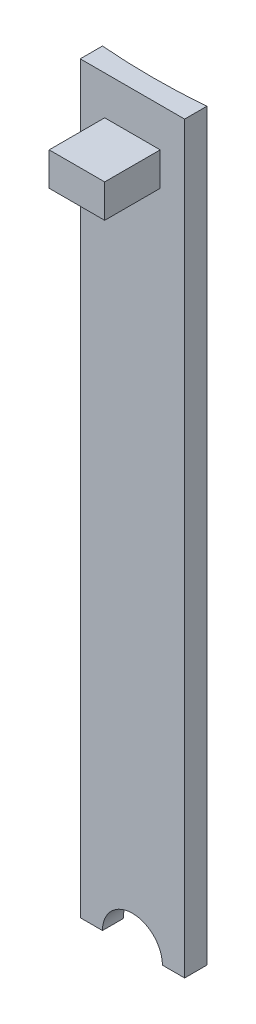
SolidWorks part; units mm, degrees
ref_plane "Front Plane" through (0, 0, 0) normal (0, 0, 1) x (1, 0, 0)
ref_plane "Top Plane" through (0, 0, 0) normal (0, 1, 0) x (1, 0, 0)
ref_plane "Right Plane" through (0, 0, 0) normal (1, 0, 0) x (0, 0, -1)
sketch "Sketch1" plane through (0, 0, 0) normal (0, 0, 1) x (1, 0, 0)
  line L0 (-2.7, -32.5) -> (-4.7, -32.5)
  line L1 (2.7, 32.5) -> (-2.7, 32.5)
  line L2 (2.7, 32.5) -> (2.7, -32.5)
  line L4 (-2.7, 32.5) -> (-2.7, -32.5)
  line L5 (2.7, 32.5) -> (-2.7, -32.5) construction
  line L6 (2.7, -32.5) -> (-2.7, 32.5) construction
  line L7 (-4.7, -32.5) -> (-4.7, 34.5)
  line L8 (-4.7, 34.5) -> (4.7, 34.5)
  line L9 (4.7, 34.5) -> (4.7, -32.5)
  line L10 (4.7, -32.5) -> (2.7, -32.5)
  line L11 (0, 29.2386) -> (0, -29.2386) construction
  arc A2 (-2.7, -32.5) -> (2.7, -32.5) centre (0, -32.5) cw
  point P0 (0, 0)
  point P13 (0, 0)
  dimension "D1" = 2.7
  dimension "D3" = 2
  dimension "D2" = 65
  dimension "D4" = 2
extrude "Boss-Extrude1" add sketch "Sketch1" along normal mid plane 2 contours L4 A2 L2 L1 | L10 L9 L8 L7 L0 L4 L1 L2
sketch "Sketch2" plane through (0, 0, 0) normal (0, 1, 0) x (1, 0, 0)
  line L4 (4.7, 1) -> (-4.7, 1)
  line L5 (-4.7, 1) -> (-4.7, -1)
  line L6 (-4.7, -1) -> (4.7, -1)
  line L7 (4.7, -1) -> (4.7, 1)
  line L8 (4.7, 1) -> (-4.7, 1)
  line L9 (-4.7, 1) -> (-4.7, -1)
  line L10 (-4.7, -1) -> (4.7, -1)
  line L11 (4.7, -1) -> (4.7, 1)
  circle A0 centre (0, 57.8059) radius 57
  point P8 (0, 1)
  dimension "D2" = 114
  dimension "D1" = 0
extrude "Cut-Extrude2" cut sketch "Sketch2" against normal through all both and the other way through all contours L8 A0
sketch "Sketch3" plane through (0, 0, 1) normal (0, 0, 1) x (1, 0, 0)
  line L1 (-2.5, 31) -> (2.5, 31)
  line L2 (-2.5, 31) -> (-2.5, 28)
  line L3 (-2.5, 28) -> (2.5, 28)
  line L4 (2.5, 31) -> (2.5, 28)
  line L5 (-4.7, -32.5) -> (-2.7, -32.5)
  line L6 (2.7, -32.5) -> (4.7, -32.5)
  line L7 (4.7, -32.5) -> (4.7, 34.5)
  line L8 (4.7, 34.5) -> (-4.7, 34.5)
  line L9 (-4.7, 34.5) -> (-4.7, -32.5)
  line L10 (-4.7, -32.5) -> (-2.7, -32.5)
  line L11 (2.7, -32.5) -> (4.7, -32.5)
  line L12 (4.7, -32.5) -> (4.7, 34.5)
  line L13 (4.7, 34.5) -> (-4.7, 34.5)
  line L14 (-4.7, 34.5) -> (-4.7, -32.5)
  line L15 (-2.5, 31) -> (2.5, 28) construction
  line L16 (-2.5, 28) -> (2.5, 31) construction
  arc A1 (2.7, -32.5) -> (-2.7, -32.5) centre (0, -32.5) ccw
  arc A2 (2.7, -32.5) -> (-2.7, -32.5) centre (0, -32.5) ccw
  point P2 (0, 29.5)
  point P12 (0, 34.5)
  dimension "D2" = 5
  dimension "D3" = 5
  dimension "D4" = 3
  dimension "D1" = 0
extrude "Boss-Extrude2" add sketch "Sketch3" along normal blind 5 contours L2 L1 L4 L3
